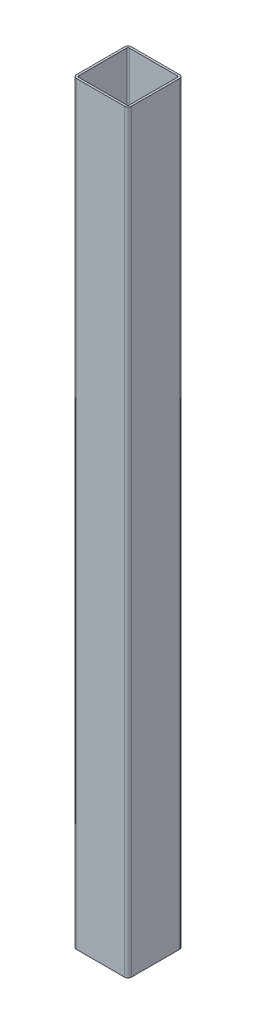
SolidWorks part; units mm, degrees
ref_plane "Спереди" through (0, 0, 0) normal (0, 0, 1) x (1, 0, 0)
ref_plane "Сверху" through (0, 0, 0) normal (0, 1, 0) x (1, 0, 0)
ref_plane "Справа" through (0, 0, 0) normal (1, 0, 0) x (0, 0, -1)
sketch "Эскиз1" plane through (0, 0, 0) normal (0, 1, 0) x (1, 0, 0)
  line L1 (-35, 40) -> (35, 40)
  line L2 (-40, 35) -> (-40, -35)
  line L3 (-35, -40) -> (35, -40)
  line L4 (40, 35) -> (40, -35)
  line L5 (-40, 40) -> (40, -40) construction
  line L6 (-40, -40) -> (40, 40) construction
  arc A0 (-40, -35) -> (-35, -40) centre (-35, -35) ccw
  arc A1 (35, -40) -> (40, -35) centre (35, -35) ccw
  arc A2 (35, 40) -> (40, 35) centre (35, 35) cw
  arc A3 (-35, 40) -> (-40, 35) centre (-35, 35) ccw
  point P0 (0, 0)
  dimension "D1" = 5
extrude "Вытянуть-Тонкостенный1" add sketch "Эскиз1" along normal blind 1100 thin
